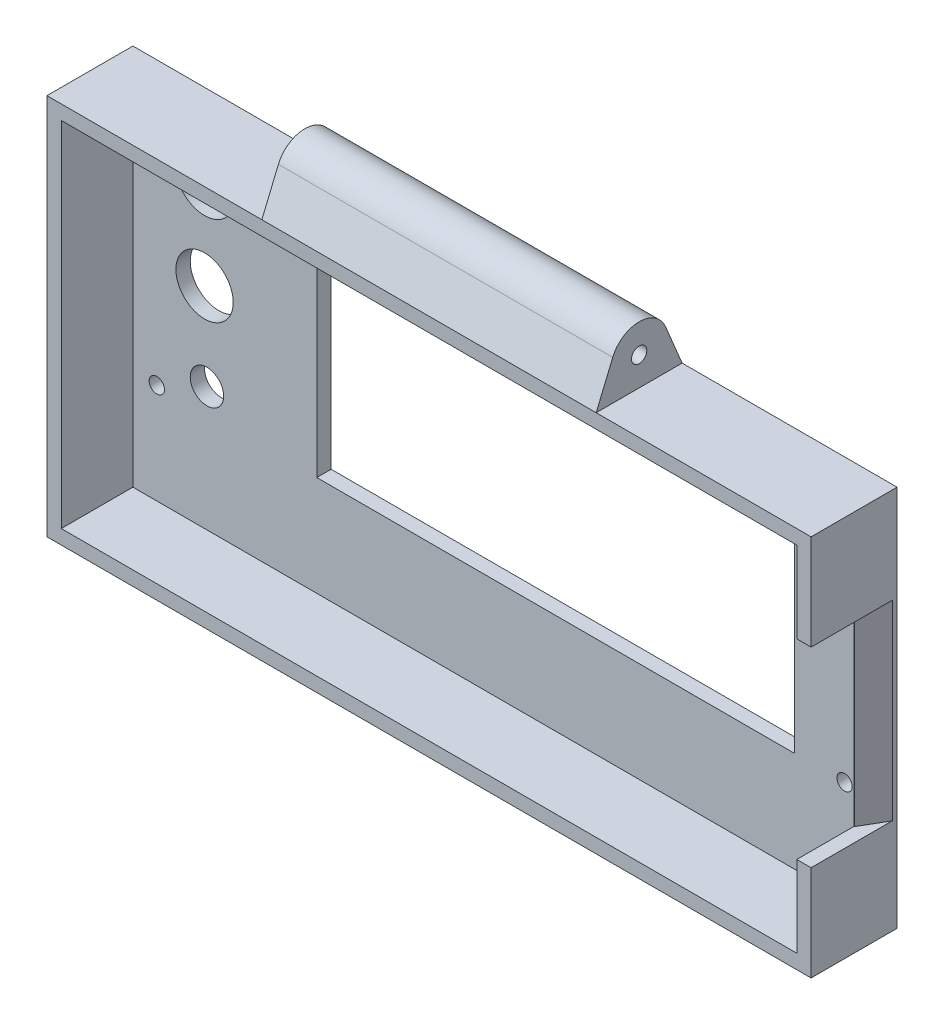
SolidWorks part; units mm, degrees
material "ABS"
ref_plane "Plano frontal" through (0, 0, 0) normal (0, 0, 1) x (1, 0, 0)
ref_plane "Plano superior" through (0, 0, 0) normal (0, 1, 0) x (1, 0, 0)
ref_plane "Plano direito" through (0, 0, 0) normal (1, 0, 0) x (0, 0, -1)
sketch "Esboço2" plane through (0, 0, 0) normal (1, 0, 0) x (0, 0, -1)
  line L0 (0, 0) -> (18, 0)
  line L2 (18, 0) -> (18, 80)
  line L3 (18, 80) -> (0, 80)
  line L4 (0, 80) -> (0, 0)
  dimension "D1" = 80
  dimension "D3" = 18
extrude "Ressalto-extrusão1" add sketch "Esboço2" along normal mid plane 160
shell "Casca1" thickness 3
sketch "Esboço4" plane through (0, 0, -18) normal (0, 0, -1) x (1, 0, 0)
  line L0 (80, -80) -> (-80, -80) construction
  line L1 (61.5, -64) -> (-38.5, -64)
  line L2 (61.5, -64) -> (61.5, -24)
  line L3 (61.5, -24) -> (-38.5, -24)
  line L4 (-38.5, -64) -> (-38.5, -24)
  line L5 (61.5, -64) -> (-38.5, -24) construction
  line L6 (61.5, -24) -> (-38.5, -64) construction
  line L8 (72, -24) -> (-72, -24) construction
  line L9 (72, -24) -> (72, -73) construction
  line L10 (72, -73) -> (-72, -73) construction
  line L11 (-72, -24) -> (-72, -73) construction
  line L12 (72, -24) -> (-72, -73) construction
  line L13 (72, -73) -> (-72, -24) construction
  circle A0 centre (-72, -24) radius 1.6
  circle A1 centre (-72, -73) radius 1.6
  circle A2 centre (72, -73) radius 1.6
  circle A3 centre (72, -24) radius 1.6
  circle A4 centre (-62, -47) radius 6
  circle A5 centre (-61.5, -29) radius 3.5
  circle A6 centre (-62, -66) radius 6.25
  point P0 (0, -48.6)
  point P9 (0, -48.5)
  dimension "D7" = 3.2
  dimension "D11" = 12
  dimension "D14" = 7
  dimension "D16" = 12.5
  dimension "D1" = 40
  dimension "D2" = 100
  dimension "D3" = 16
  dimension "D4" = 49
  dimension "D5" = 144
  dimension "D6" = 9
  dimension "D8" = 7
  dimension "D9" = 26
  dimension "D10" = 44
  dimension "D12" = 10
  dimension "D13" = 10
  dimension "D15" = 10.5
  dimension "D17" = 10.5
extrude "Corte-extrusão1" cut sketch "Esboço4" against normal up to surface (3 mm away) up to face at (0, 40, -15)
sketch "Esboço5" plane through (80, 0, 0) normal (1, 0, 0) x (0, 0, -1)
  line L0 (14.5385, 88.3077) -> (18, 80)
  line L1 (18, 80) -> (0, 80)
  line L2 (0, 80) -> (3.4615, 88.3077)
  arc A0 (14.5385, 88.3077) -> (3.4615, 88.3077) centre (9, 86) ccw
  circle A1 centre (9, 86) radius 1.6
  point P9 (9, 80)
  dimension "D1" = 12
  dimension "D2" = 3.2
extrude "Ressalto-extrusão2" add sketch "Esboço5" against normal through all
sketch "Esboço6" plane through (0, 0, -18) normal (0, 0, -1) x (-1, 0, 0)
  line L0 (-80, 80) -> (80, 80) construction
  line L1 (-35, 92) -> (35, 92) construction
  line L2 (-35, 80) -> (-35, 92)
  line L3 (35, 80) -> (80, 80)
  line L4 (35, 80) -> (35, 92)
  line L5 (35, 92) -> (80, 92)
  line L6 (-80, 80) -> (-35, 80)
  line L7 (-80, 80) -> (-80, 92)
  line L8 (-80, 92) -> (-35, 92)
  line L9 (80, 80) -> (80, 92)
  line L10 (80, 92) -> (-80, 92) construction
  line L11 (80, 0) -> (80, 80) construction
  point P6 (0, 92)
  point P8 (0, 80)
  dimension "D1" = 70
extrude "Corte-extrusão2" cut sketch "Esboço6" against normal through all
sketch "Esboço7" plane through (80, 0, 0) normal (1, 0, 0) x (0, 0, -1)
  line L0 (0, 80) -> (18, 80) construction
  line L1 (0, 60) -> (12, 60)
  line L2 (0, 60) -> (0, 20)
  line L3 (0, 20) -> (12, 20)
  line L4 (12, 60) -> (12, 20)
  line L5 (0, 80) -> (0, 0) construction
  dimension "D1" = 20
  dimension "D2" = 40
  dimension "D3" = 12
extrude "Corte-extrusão3" cut sketch "Esboço7" against normal blind 10
chamfer "Chanfro1" distance 5 angle 30 1 edges at (80, 40, -12)
